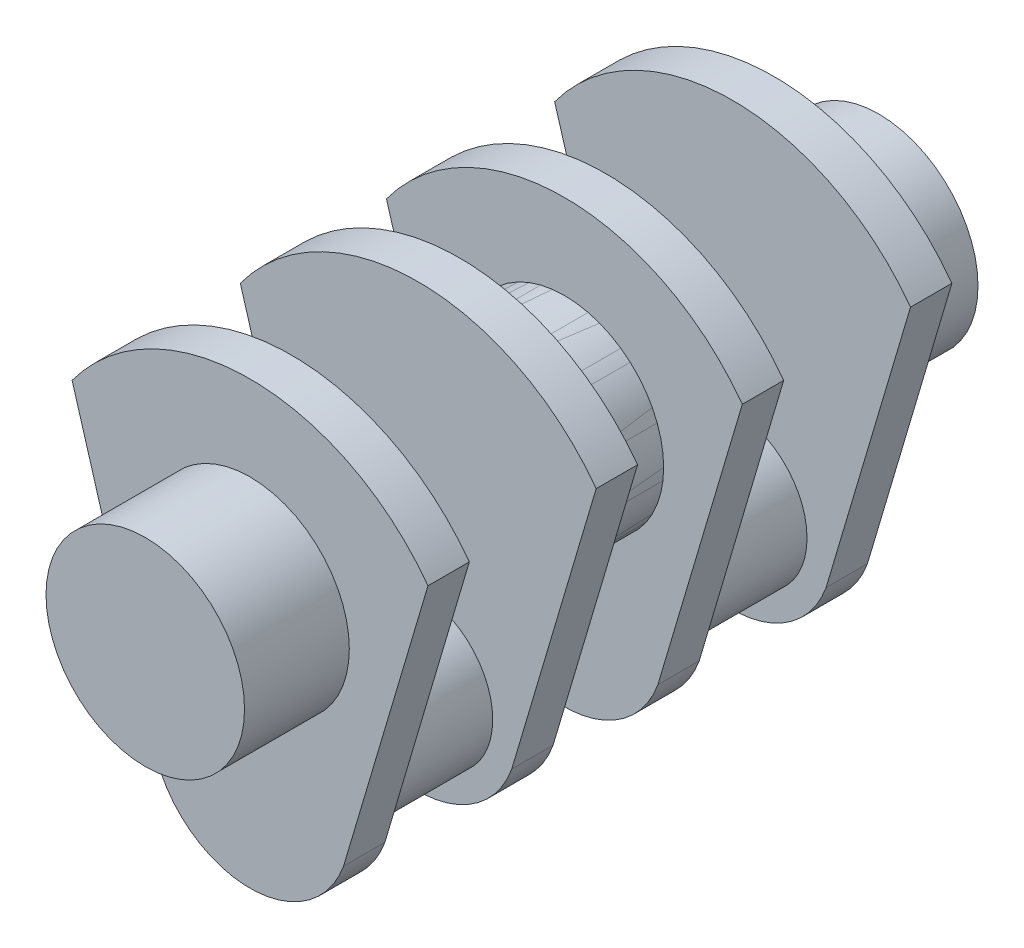
SolidWorks part; units mm, degrees
ref_plane "Front Plane" through (0, 0, 0) normal (0, 0, 1) x (1, 0, 0)
ref_plane "Top Plane" through (0, 0, 0) normal (0, 1, 0) x (1, 0, 0)
ref_plane "Right Plane" through (0, 0, 0) normal (1, 0, 0) x (0, 0, -1)
sketch "Sketch2" plane through (0, 0, 0) normal (0, 0, 1) x (1, 0, 0)
  line L0 (0, 782.014) -> (0, -1453.186) construction
  line L1 (-1715.8681, 50.6085) -> (2096.6365, 50.6085) construction
  line L2 (-1639.0739, 865.4389) -> (-861.3517, -1760.1072)
  line L3 (1639.0739, 865.4389) -> (861.3517, -1760.1072)
  circle A0 centre (0, -1453.186) radius 914.4
  arc A1 (-1639.0739, 865.4389) -> (1639.0739, 865.4389) centre (0, -335.586) cw
  dimension "D1" = 1828.8
  dimension "D3" = 2032
  dimension "D2" = 33
  dimension "D4" = 1117.6
extrude "Boss-Extrude1" add sketch "Sketch2" along normal blind 381 contours A1 L2 A0 L3 | L2 A0 L3
sketch "Sketch3" plane through (0, 0, 0) normal (0, 0, -1) x (-1, 0, 0)
  circle A0 centre (0, -1453.186) radius 685.8
  dimension "D1" = 1371.6
extrude "Boss-Extrude2" add sketch "Sketch3" along normal blind 1168.4
sketch "Sketch4" plane through (0, 0, 381) normal (0, 0, 1) x (1, 0, 0)
  circle A0 centre (0, 0) radius 914.4
  dimension "D1" = 1828.8
extrude "Boss-Extrude3" add sketch "Sketch4" along normal blind 965.2
ref_plane "Plane3" through (0, 0, -584.2) normal (0, 0, -1) x (-1, 0, 0)
mirror "Mirror1" about plane through (0, 0, -584.2) normal (0, 0, -1) of bodies 103
ref_plane "Plane4" through (0, 0, -2032) normal (0, 0, -1) x (-1, 0, 0)
mirror "Mirror2" about plane through (0, 0, -2032) normal (0, 0, -1) of bodies 104
